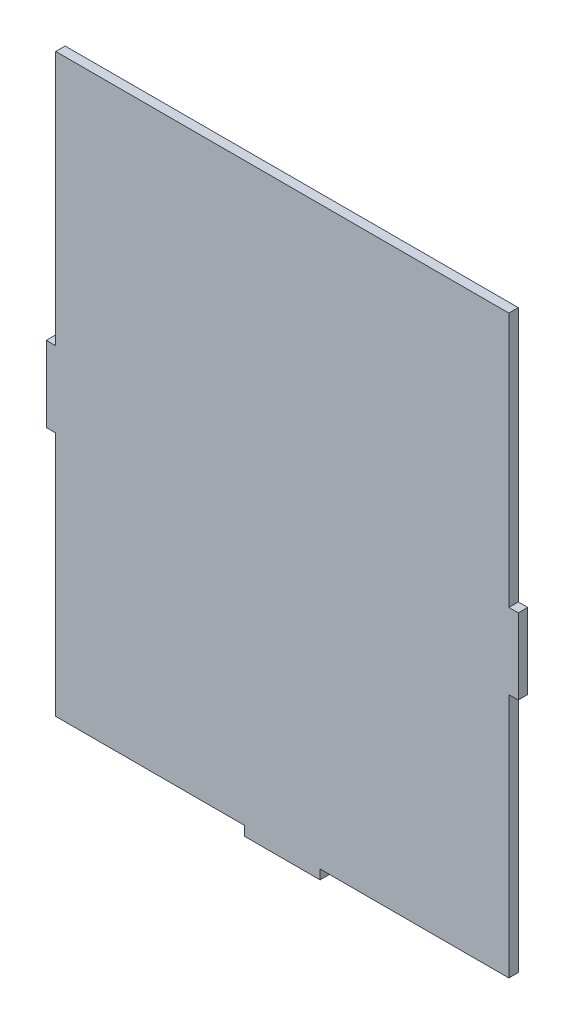
SolidWorks part; units mm, degrees
ref_plane "Plan de face" through (0, 0, 0) normal (0, 0, 1) x (1, 0, 0)
ref_plane "Plan de dessus" through (0, 0, 0) normal (0, 1, 0) x (1, 0, 0)
ref_plane "Plan de droite" through (0, 0, 0) normal (1, 0, 0) x (0, 0, -1)
sketch "Esquisse1" plane through (0, 0, 0) normal (0, 0, 1) x (1, 0, 0)
  line L13 (0, -140) -> (348.1503, -140) construction
  line L21 (5, 15) -> (245, 15)
  line L22 (0, -120) -> (0, -160)
  line L23 (105, -295) -> (145, -295)
  line L24 (250, -120) -> (250, -160)
  line L25 (125, 0) -> (125, -362.0025) construction
  line L26 (5, 15) -> (5, -120)
  line L27 (5, -120) -> (0, -120)
  line L28 (0, -160) -> (5, -160)
  line L29 (5, -160) -> (5, -290)
  line L30 (5, -290) -> (105, -290)
  line L31 (105, -290) -> (105, -295)
  line L32 (145, -290) -> (145, -295)
  line L33 (145, -290) -> (245, -290)
  line L34 (245, 15) -> (245, -120)
  line L35 (245, -120) -> (250, -120)
  line L36 (250, -160) -> (245, -160)
  line L37 (245, -160) -> (245, -290)
  dimension "D1" = 5
  dimension "D2" = 20
  dimension "D3" = 125
  dimension "D4" = 155
  dimension "D5" = 5
  dimension "D6" = 20
  dimension "D7" = 20
  dimension "D8" = 20
  dimension "D9" = 5
  dimension "D10" = 310
extrude "Boss.-Extru.1" add sketch "Esquisse1" along normal blind 5
